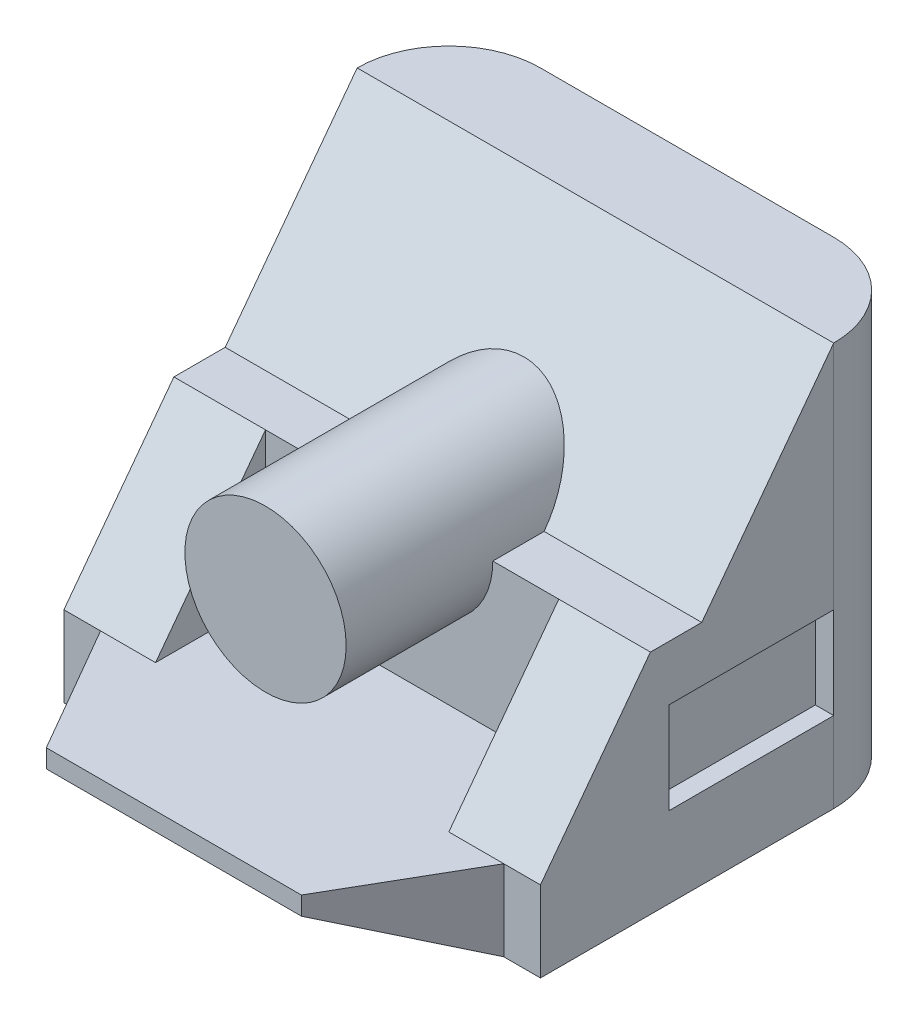
SolidWorks part; units mm, degrees
ref_plane "Front Plane" through (0, 0, 0) normal (0, 0, 1) x (1, 0, 0)
ref_plane "Top Plane" through (0, 0, 0) normal (0, 1, 0) x (1, 0, 0)
ref_plane "Right Plane" through (0, 0, 0) normal (1, 0, 0) x (0, 0, -1)
sketch "Sketch1" plane through (0, 0, 0) normal (1, 0, 0) x (0, 0, -1)
  line L0 (0, 0) -> (0, 110)
  line L1 (0, 110) -> (-25, 110)
  line L2 (-25, 110) -> (-61, 62)
  line L3 (-61, 62) -> (-75, 62)
  line L4 (-75, 62) -> (-105, 22)
  line L5 (-105, 22) -> (-140, 22)
  line L6 (-140, 17) -> (-105, 0)
  line L7 (-105, 0) -> (0, 0)
  line L8 (-140, 22) -> (-140, 17)
  dimension "D1" = 110
  dimension "D2" = 5
  dimension "D3" = 14
  dimension "D4" = 35
  dimension "D5" = 25
  dimension "D6" = 30
  dimension "D7" = 35
  dimension "D8" = 36
  dimension "D9" = 22
extrude "Extrude1" add sketch "Sketch1" along normal blind 130
fillet "Fillet1" radius 25 2 edges at (0, 55, 0) (130, 55, 0)
sketch "Sketch2" plane through (0, 22, 0) normal (0, 1, 0) x (1, 0, 0)
  line L0 (99.7927, -140) -> (130, -140)
  line L1 (130, -140) -> (0, -140) construction
  line L2 (130, -140) -> (130, -105)
  line L3 (130, -105) -> (120, -105)
  line L4 (130, -105) -> (0, -105) construction
  line L5 (120, -105) -> (99.7927, -140)
  line L6 (65, -140) -> (65, -105) construction
  line L7 (10, -105) -> (30.2073, -140)
  line L8 (30.2073, -140) -> (0, -140)
  line L9 (0, -140) -> (0, -105)
  line L10 (0, -105) -> (10, -105)
  dimension "D1" = 60
  dimension "D2" = 10
extrude "Extrude2" cut sketch "Sketch2" against normal blind 130
sketch "Sketch3" plane through (130, 0, 0) normal (1, 0, 0) x (0, 0, -1)
  line L0 (-25, 0) -> (-25, 110) construction
  line L1 (-25, 47) -> (-70, 47)
  line L2 (-25, 47) -> (-25, 22)
  line L3 (-25, 22) -> (-70, 22)
  line L4 (-70, 47) -> (-70, 22)
  line L5 (-61, 62) -> (-75, 62) construction
  line L6 (-105, 0) -> (-25, 0) construction
  dimension "D1" = 15
  dimension "D2" = 45
  dimension "D3" = 22
extrude "Extrude3" cut sketch "Sketch3" against normal blind 5
sketch "Sketch4" plane through (0, 62, 0) normal (0, 1, 0) x (1, 0, 0)
  line L0 (130, -75) -> (0, -75) construction
  line L1 (25, -75) -> (105, -75)
  line L2 (25, -75) -> (25, -105)
  line L3 (25, -105) -> (105, -105)
  line L4 (105, -75) -> (105, -105)
  line L5 (120, -105) -> (10, -105) construction
  line L6 (130, -75) -> (130, -105) construction
  line L7 (0, -75) -> (0, -105) construction
  dimension "D1" = 25
  dimension "D2" = 25
extrude "Extrude4" cut sketch "Sketch4" against normal up to surface (40 mm away) up to face at (65, 22, 122.5)
sketch "Sketch5" plane through (0, 0, 75) normal (0, 0, 1) x (1, 0, 0)
  line L0 (130, 62) -> (0, 62) construction
  circle A0 centre (65, 62) radius 22
  dimension "D1" = 44
extrude "Extrude5" add sketch "Sketch5" along normal blind 40 and the other way up to surface other way up to face at (65, 86, 43)
